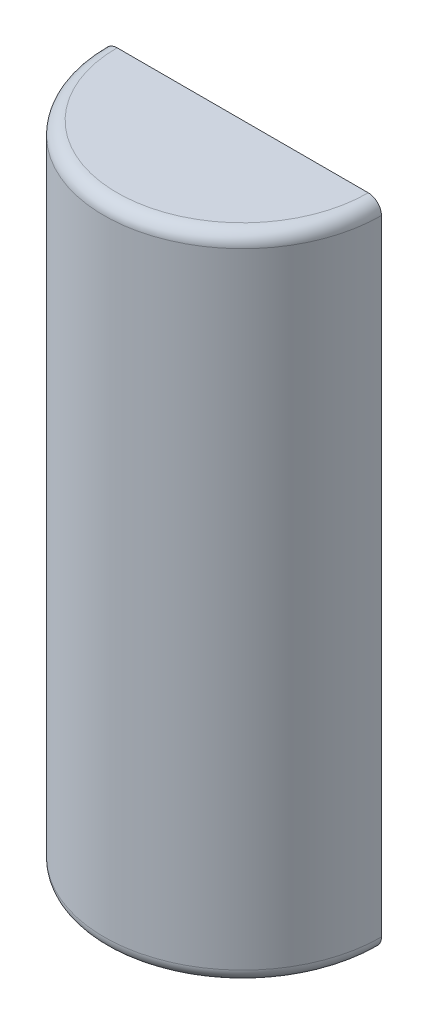
SolidWorks part; units mm, degrees
material "Custom Plastic"
ref_plane "Front Plane" through (0, 0, 0) normal (0, 0, 1) x (1, 0, 0)
ref_plane "Top Plane" through (0, 0, 0) normal (0, 1, 0) x (1, 0, 0)
ref_plane "Right Plane" through (0, 0, 0) normal (1, 0, 0) x (0, 0, -1)
sketch "Sketch1" plane through (0, 0, 0) normal (0, 0, 1) x (1, 0, 0)
  line L0 (0, 0) -> (0, 628.8) construction
  line L2 (0, 0) -> (-133.985, 0)
  line L3 (0, 0) -> (0, 628.8)
  line L4 (0, 628.8) -> (-133.985, 628.8)
  line L5 (-133.985, 0) -> (-133.985, 628.8)
  dimension "D1" = 628.8
  dimension "D2" = 133.985
revolve "Revolve1" add sketch "Sketch1" angle 180 about L0
fillet "Fillet1" radius 12.7 2 edges at (0, 0, 133.985) (0, 628.8, 133.985)
